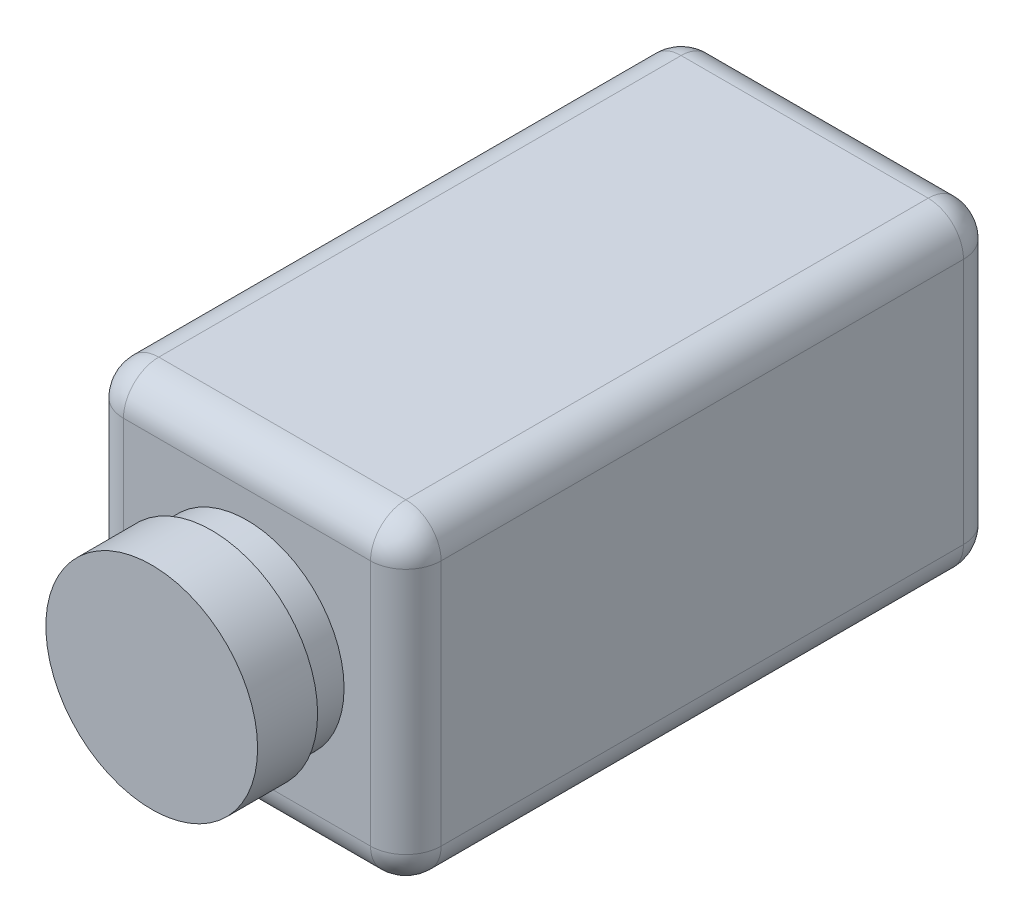
SolidWorks part; units mm, degrees
ref_plane "정면" through (0, 0, 0) normal (0, 0, 1) x (1, 0, 0)
ref_plane "윗면" through (0, 0, 0) normal (0, 1, 0) x (1, 0, 0)
ref_plane "우측면" through (0, 0, 0) normal (1, 0, 0) x (0, 0, -1)
sketch "스케치1" plane through (0, 0, 0) normal (0, 0, 1) x (1, 0, 0)
  line L1 (0, 0) -> (90, 0)
  line L2 (0, 0) -> (0, -90)
  line L3 (0, -90) -> (90, -90)
  line L4 (90, 0) -> (90, -90)
  dimension "D1" = 90
  dimension "D2" = 90
extrude "보스-돌출1" add sketch "스케치1" along normal blind 168
fillet "필렛1" radius 10 12 edges at (45, -90, 168) (45, -90, 0) (0, -45, 168) (0, -90, 84) (0, -45, 0) (45, 0, 168) (0, 0, 84) (45, 0, 0) (90, -90, 84) (90, -45, 168) (90, 0, 84) (90, -45, 0)
sketch "스케치2" plane through (0, 0, 168) normal (0, 0, 1) x (1, 0, 0)
  line L0 (10, -80) -> (80, -80) construction
  line L3 (80, -80) -> (80, -10) construction
  circle A0 centre (45, -45) radius 27.5
  dimension "D2" = 55
  dimension "D1" = 35
  dimension "D3" = 35
extrude "보스-돌출2" add sketch "스케치2" along normal blind 10
sketch "스케치3" plane through (0, 0, 178) normal (0, 0, 1) x (1, 0, 0)
  circle A0 centre (45, -45) radius 30
  dimension "D1" = 60
extrude "보스-돌출3" add sketch "스케치3" along normal blind 17
